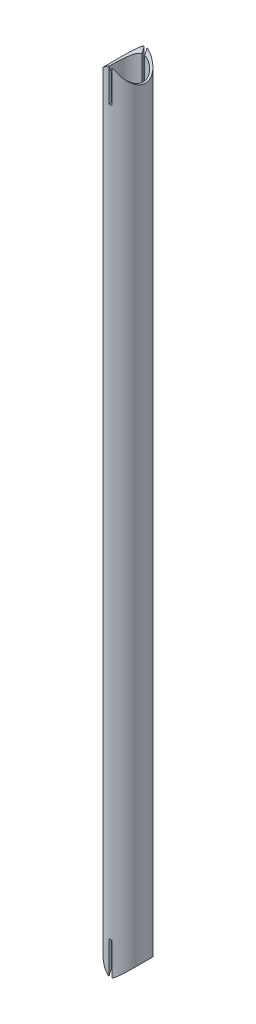
SolidWorks part; units mm, degrees
material "1.7218 (25CrMo4)"
ref_plane "Płaszczyzna XY" through (0, 0, 0) normal (0, 0, 1) x (1, 0, 0)
ref_plane "Płaszczyzna XZ" through (0, 0, 0) normal (0, 1, 0) x (1, 0, 0)
ref_plane "Płaszczyzna YZ" through (0, 0, 0) normal (1, 0, 0) x (0, 0, -1)
sketch "Sketch1" plane through (0, 0, 0) normal (0, 1, 0) x (1, 0, 0)
  circle A0 centre (0, 0) radius 12.7
  circle A1 centre (0, 0) radius 11.05
  dimension "D1" = 25.4
  dimension "D2" = 22.1
extrude "Boss-Extrude1" add sketch "Sketch1" along normal mid plane 575
sketch3d "3DSketch1"
  line L0 (0, 287.5, 0) -> (0, -287.5, 0)
  line L2 (0, -287.5, 0) -> (-105, -287.5, 0)
  line L3 (0, 287.5, 0) -> (-105, 287.5, 0)
  point P4 (0, 0, 0)
  dimension "D1" = 575
  dimension "D3" = 105
  dimension "D4" = 105
sketch "Sketch2" plane through (0, 0, 0) normal (1, 0, 0) x (0, 0, -1)
  circle A0 centre (0, -287.5) radius 13
  dimension "D1" = 26
extrude "Cut-Extrude1" cut sketch "Sketch2" against normal through all both and the other way through all
mirror "Mirror1" about plane through (0, 0, 0) normal (0, 1, 0) of "Cut-Extrude1"
sketch "Sketch3" plane through (0, 0, 0) normal (0, 0, 1) x (1, 0, 0)
  line L1 (-1, -314) -> (1, -314)
  line L2 (-1, -314) -> (-1, -261)
  line L3 (-1, -261) -> (1, -261)
  line L4 (1, -314) -> (1, -261)
  line L5 (-1, -314) -> (1, -261) construction
  line L6 (-1, -261) -> (1, -314) construction
  point P0 (0, -287.5)
  dimension "D1" = 2
  dimension "D2" = 53
extrude "Cut-Extrude2" cut sketch "Sketch3" against normal through all both and the other way through all
mirror "Mirror2" about plane through (0, 0, 0) normal (0, 1, 0) of "Cut-Extrude2"
